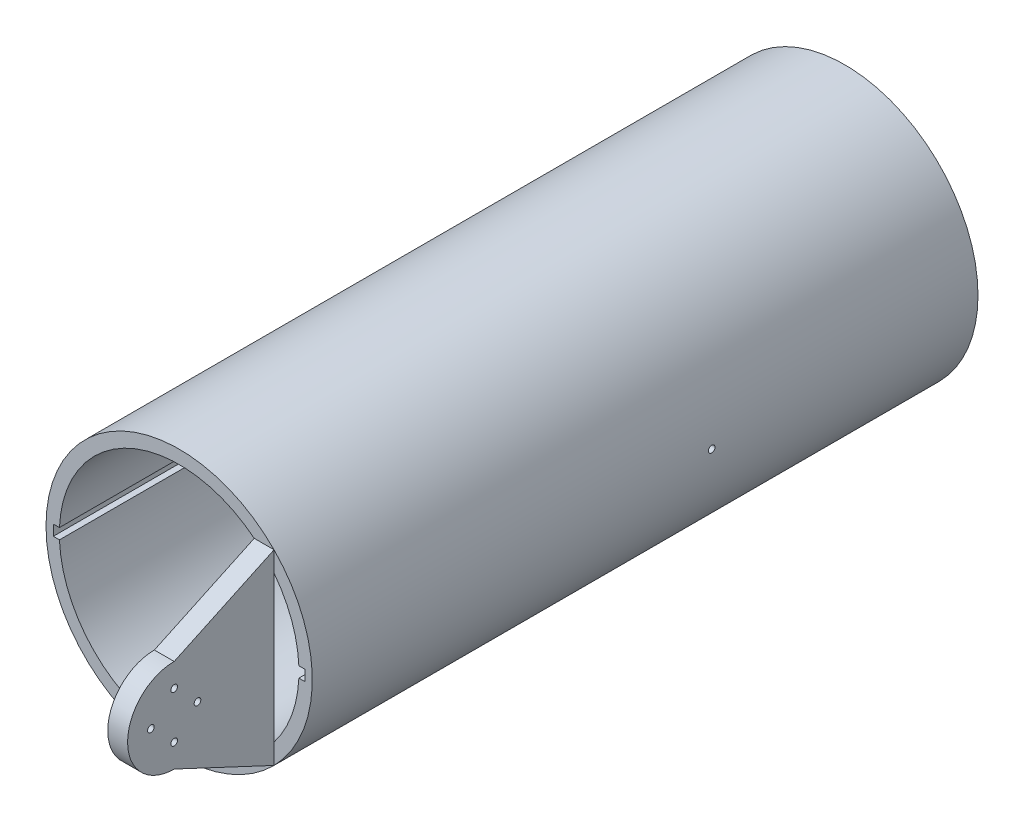
SolidWorks part; units mm, degrees
ref_plane "Front Plane" through (0, 0, 0) normal (0, 0, 1) x (1, 0, 0)
ref_plane "Top Plane" through (0, 0, 0) normal (0, 1, 0) x (1, 0, 0)
ref_plane "Right Plane" through (0, 0, 0) normal (1, 0, 0) x (0, 0, -1)
sketch "Sketch1" plane through (0, 0, 0) normal (0, 0, 1) x (1, 0, 0)
  line L0 (0, 45) -> (0, -22.6804) construction
  line L1 (-44.9556, 1.9995) -> (-47.2556, 1.9995)
  line L2 (-47.2556, 1.9995) -> (-47.2556, -1.9995)
  line L3 (44.9556, -1.9995) -> (47.2556, -1.9995)
  line L4 (-44.9556, -1.9995) -> (-47.2556, -1.9995)
  line L5 (47.2556, 1.9995) -> (47.2556, -1.9995)
  line L6 (44.9556, 1.9995) -> (47.2556, 1.9995)
  circle A0 centre (0, 0) radius 50
  arc A1 (-44.9556, -1.9995) -> (44.9556, -1.9995) centre (0, 0) ccw
  arc A2 (44.9556, 1.9995) -> (-44.9556, 1.9995) centre (0, 0) ccw
extrude "Boss-Extrude1" add sketch "Sketch1" along normal blind 250
sketch "Sketch3" plane through (0, 0, 250) normal (0, 0, 1) x (1, 0, 0)
  line L0 (0, 0) -> (28.2, 0) construction
  line L1 (28.2, 0) -> (28.2, 35.0679)
  line L2 (28.2, 35.0679) -> (35.6404, 35.0679)
  line L3 (35.6404, 35.0679) -> (35.6404, -35.0679)
  line L4 (35.6404, -35.0679) -> (28.2, -35.0679)
  line L5 (28.2, -35.0679) -> (28.2, 0)
  arc A0 (44.9556, 1.9995) -> (-44.9556, 1.9995) centre (0, 0) ccw construction
  circle A1 centre (0, 0) radius 50 construction
  arc A2 (-44.9556, -1.9995) -> (44.9556, -1.9995) centre (0, 0) ccw construction
extrude "Boss-Extrude2" add sketch "Sketch3" along normal blind 55
sketch "Sketch7" plane through (35.6404, 0, 0) normal (1, 0, 0) x (0, 0, -1)
  line L0 (-250, 0) -> (-100, 0) construction
  line L1 (-250, -27.4729) -> (-250, 27.4729) construction
  circle A0 centre (-100, 0) radius 1.25
extrude "Cut-Extrude4" cut sketch "Sketch7" against normal blind 96 and the other way blind 75
sketch "Sketch8" plane through (35.6404, 0, 0) normal (1, 0, 0) x (0, 0, -1)
  line L0 (-305, 0) -> (-287.5, 0) construction
  line L1 (-305, -35.0679) -> (-305, 35.0679) construction
  line L2 (-287.5, 0) -> (-270, 0) construction
  line L3 (-287.5, 17.5) -> (-250, 35.0679)
  line L4 (-250, 35.0679) -> (-305, 35.0679)
  line L5 (-305, 35.0679) -> (-305, 0)
  arc A0 (-287.5, 17.5) -> (-305, 0) centre (-287.5, 0) ccw
extrude "Cut-Extrude5" cut sketch "Sketch8" against normal blind 96
sketch "Sketch9" plane through (35.6404, 0, 0) normal (1, 0, 0) x (0, 0, -1)
  line L0 (-287.5, -17.5) -> (-250, -35.0679)
  line L1 (-250, -35.0679) -> (-305, -35.0679)
  line L2 (-305, -35.0679) -> (-305, 0)
  arc A0 (-305, 0) -> (-287.5, -17.5) centre (-287.5, 0) ccw
extrude "Cut-Extrude6" cut sketch "Sketch9" against normal blind 96
sketch "Sketch10" plane through (35.6404, 0, 0) normal (1, 0, 0) x (0, 0, -1)
  line L0 (-287.5, 17.5) -> (-287.5, 0) construction
  line L1 (-287.5, 0) -> (-287.5, -17.5) construction
  line L2 (-305, 0) -> (-287.5, 0) construction
  line L3 (-287.5, 0) -> (-270, 0) construction
  arc A0 (-287.5, 17.5) -> (-287.5, -17.5) centre (-287.5, 0) ccw construction
  circle A1 centre (-296.25, 0) radius 1.25
  circle A2 centre (-287.5, 8.75) radius 1.25
  circle A3 centre (-278.75, 0) radius 1.25
  circle A4 centre (-287.5, -8.75) radius 1.25
extrude "Cut-Extrude7" cut sketch "Sketch10" against normal blind 96
